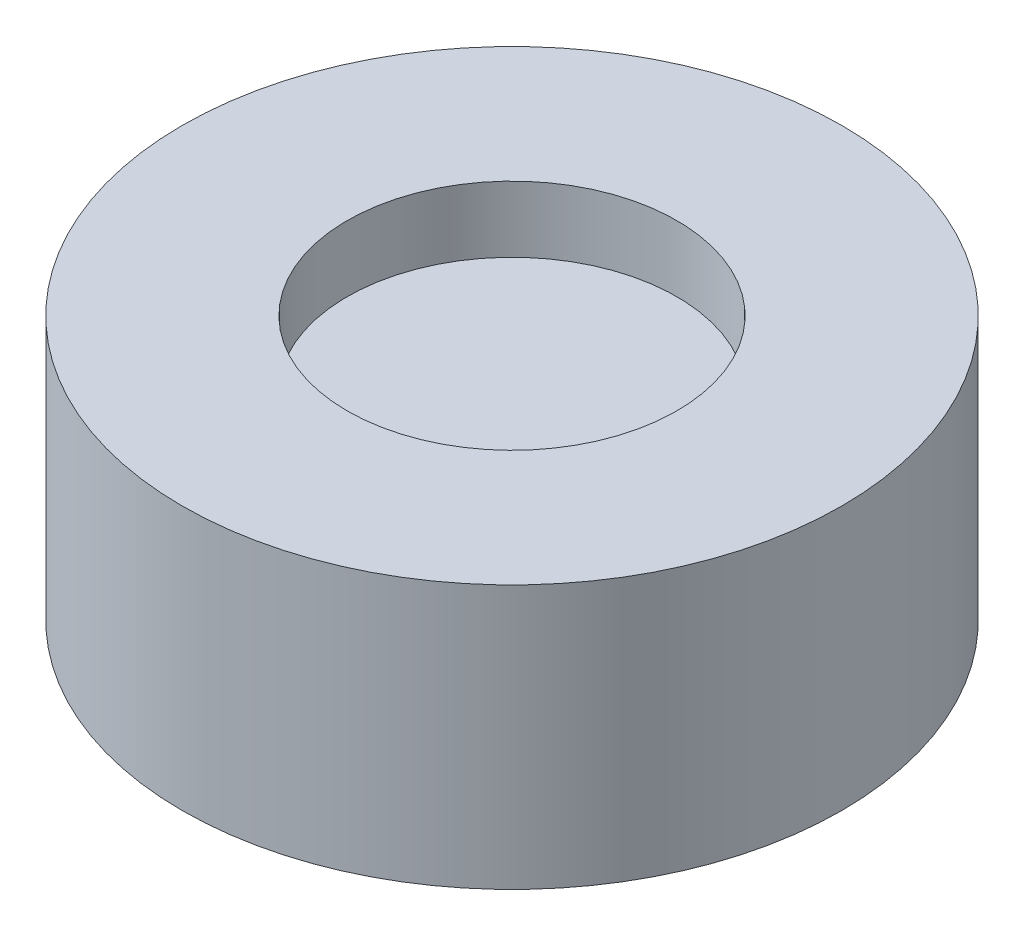
SolidWorks part; units mm, degrees
ref_plane "Front Plane" through (0, 0, 0) normal (0, 0, 1) x (1, 0, 0)
ref_plane "Top Plane" through (0, 0, 0) normal (0, 1, 0) x (1, 0, 0)
ref_plane "Right Plane" through (0, 0, 0) normal (1, 0, 0) x (0, 0, -1)
sketch "Sketch1" plane through (0, 0, 0) normal (0, 1, 0) x (1, 0, 0)
  circle A0 centre (0, 0) radius 10
  dimension "D1" = 20
extrude "Boss-Extrude1" add sketch "Sketch1" along normal blind 8
sketch "Sketch2" plane through (0, 8, 0) normal (0, 1, 0) x (1, 0, 0)
  circle A0 centre (0, 0) radius 5
  dimension "D1" = 10
extrude "Cut-Extrude1" cut sketch "Sketch2" against normal blind 2
sketch "Sketch3" plane through (0, 0, 0) normal (0, -1, 0) x (1, 0, 0)
  circle A0 centre (0, 0) radius 1
  dimension "D1" = 2
extrude "Cut-Extrude2" cut sketch "Sketch3" against normal blind 2
fillet "Fillet1" radius 1 1 edges at (0, 2, -1)
